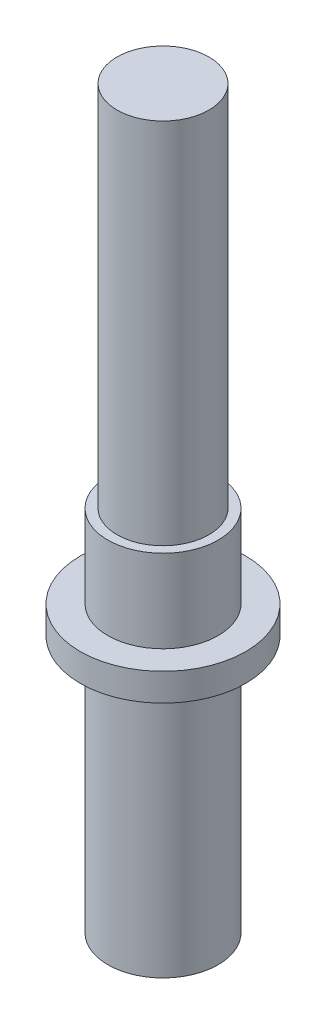
SolidWorks part; units mm, degrees
material "AISI 1020"
ref_plane "Front Plane" through (0, 0, 0) normal (0, 0, 1) x (1, 0, 0)
ref_plane "Top Plane" through (0, 0, 0) normal (0, 1, 0) x (1, 0, 0)
ref_plane "Right Plane" through (0, 0, 0) normal (1, 0, 0) x (0, 0, -1)
sketch "Sketch1" plane through (0, 0, 0) normal (0, 0, 1) x (1, 0, 0)
  line L0 (0, 0) -> (0, 40) construction
  line L1 (0, 0) -> (3, 0)
  line L2 (3, 0) -> (3, 14)
  line L3 (3, 14) -> (4.5, 14)
  line L4 (4.5, 14) -> (4.5, 15.5)
  line L5 (4.5, 15.5) -> (3, 15.5)
  line L6 (3, 15.5) -> (3, 20)
  line L7 (3, 20) -> (2.5, 20)
  line L8 (2.5, 20) -> (2.5, 40)
  line L9 (2.5, 40) -> (0, 40)
  line L10 (0, 0) -> (0, 40)
  dimension "D1" = 40
  dimension "D2" = 20
  dimension "D3" = 4.5
  dimension "D4" = 1.5
  dimension "D5" = 2.5
  dimension "D6" = 3
  dimension "D7" = 4.5
  dimension "D8" = 3
revolve "Revolve1" add sketch "Sketch1" angle 360 about L0
